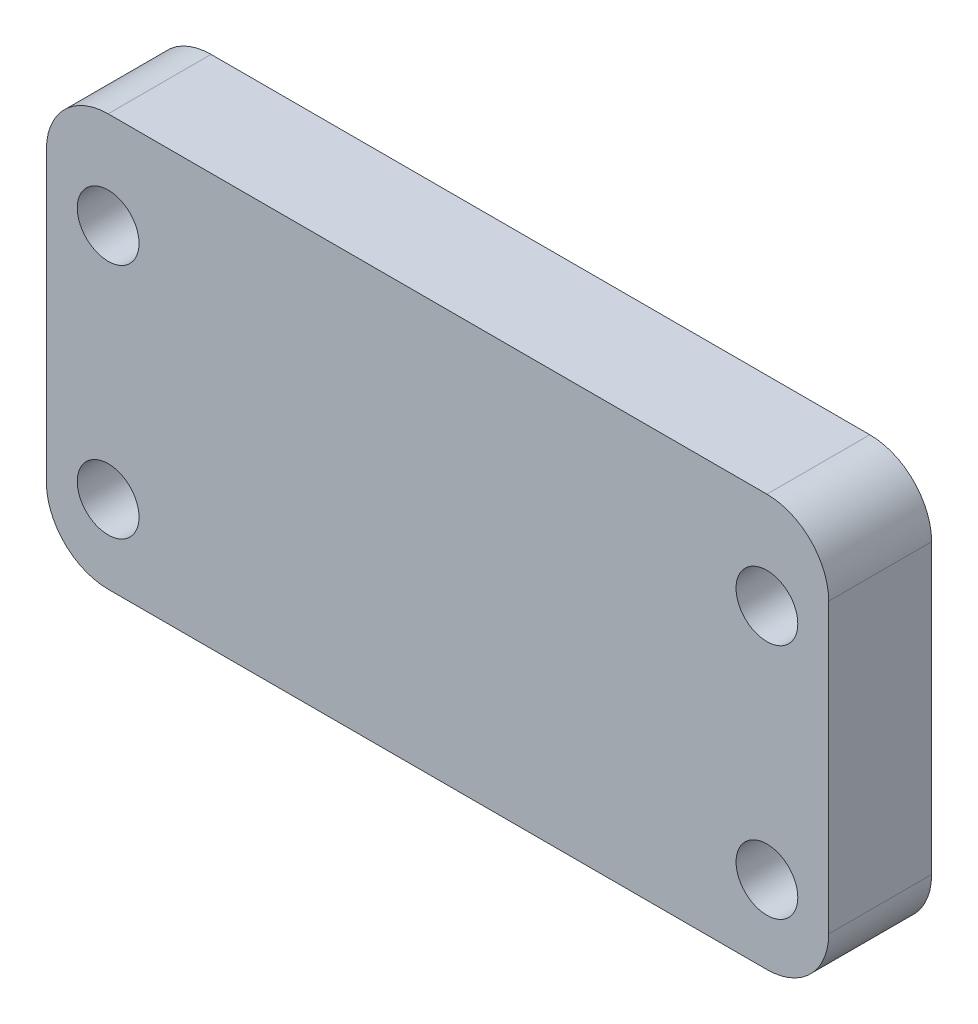
SolidWorks part; units mm, degrees
material "Acrylic (Medium-high impact)"
ref_plane "Front Plane" through (0, 0, 0) normal (0, 0, 1) x (1, 0, 0)
ref_plane "Top Plane" through (0, 0, 0) normal (0, 1, 0) x (1, 0, 0)
ref_plane "Right Plane" through (0, 0, 0) normal (1, 0, 0) x (0, 0, -1)
sketch "Sketch1" plane through (0, 0, 0) normal (0, 0, 1) x (1, 0, 0)
  line L0 (20.8893, 19.8664) -> (20.8893, -0.1336) construction
  line L1 (-14.1107, -0.1336) -> (23.8893, -0.1336)
  line L2 (-14.1107, -0.1336) -> (-14.1107, 19.8664)
  line L3 (-14.1107, 19.8664) -> (23.8893, 19.8664)
  line L4 (23.8893, -0.1336) -> (23.8893, 19.8664)
  line L5 (4.8893, 19.8664) -> (4.8893, -0.1336) construction
  line L6 (-11.1107, 19.8664) -> (-11.1107, -0.1336) construction
  line L7 (-14.1107, 15.1629) -> (23.8893, 15.1629) construction
  line L8 (-14.1107, 3.6515) -> (23.8893, 3.6515) construction
  circle A1 centre (-11.1107, 15.1629) radius 1.5
  circle A2 centre (-11.1107, 3.6515) radius 1.5
  circle A3 centre (20.8893, 15.1629) radius 1.5
  circle A4 centre (20.8893, 3.6515) radius 1.5
  dimension "D5" = 3
  dimension "D6" = 3
  dimension "D7" = 3
  dimension "D8" = 3
  dimension "D1" = 38
  dimension "D2" = 20
  dimension "D3" = 3
  dimension "D4" = 3
extrude "Boss-Extrude1" add sketch "Sketch1" along normal blind 5
fillet "Fillet1" radius 3 1 edges at (23.8893, 19.8664, 2.5)
fillet "Fillet2" radius 3 1 edges at (23.8893, -0.1336, 2.5)
fillet "Fillet3" radius 3 1 edges at (-14.1107, -0.1336, 2.5)
fillet "Fillet4" radius 3 1 edges at (-14.1107, 19.8664, 2.5)
